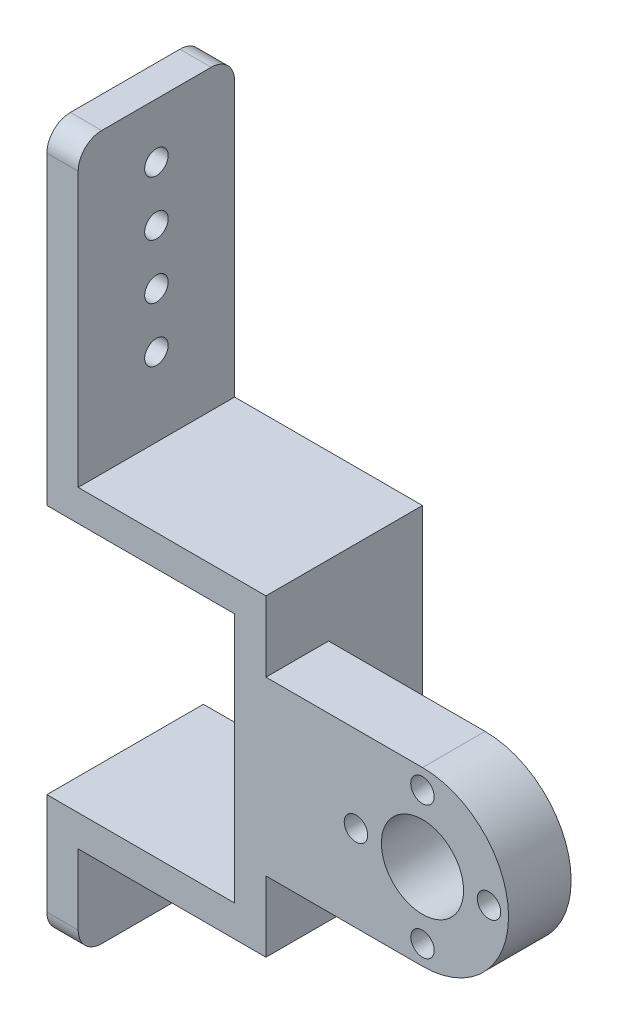
SolidWorks part; units mm, degrees
ref_plane "Front Plane" through (0, 0, 0) normal (0, 0, 1) x (1, 0, 0)
ref_plane "Top Plane" through (0, 0, 0) normal (0, 1, 0) x (1, 0, 0)
ref_plane "Right Plane" through (0, 0, 0) normal (1, 0, 0) x (0, 0, -1)
sketch "Sketch1" plane through (0, 0, 0) normal (0, 0, 1) x (1, 0, 0)
  line L1 (-12, -11) -> (12, -11)
  line L2 (-12, -11) -> (-12, 11)
  line L3 (-12, 11) -> (12, 11)
  line L4 (12, -11) -> (12, 11)
  line L5 (-12, -11) -> (12, 11) construction
  line L6 (-12, 11) -> (12, -11) construction
  circle A0 centre (12, 0) radius 11
  point P0 (0, 0)
  dimension "D1" = 24
  dimension "D2" = 22
extrude "Boss-Extrude2" add sketch "Sketch1" along normal blind 8 contours L4 A0 | L4 A0 | A0 L3 L2 L1
sketch "Sketch3" plane through (0, 0, 8) normal (0, 0, 1) x (1, 0, 0)
  circle A0 centre (12, 0) radius 5.25
  dimension "D1" = 10.5
extrude "Cut-Extrude1" cut sketch "Sketch3" against normal blind 8
sketch "Sketch7" plane through (0, 0, 8) normal (0, 0, 1) x (1, 0, 0)
  line L0 (-12, 11) -> (-12, 20)
  line L1 (-12, 20) -> (-8, 20)
  line L2 (-8, 20) -> (-8, 11)
  line L3 (-12, 11) -> (12, 11) construction
  line L4 (-8, 11) -> (-12, 11)
  line L5 (-12, -11) -> (-12, -20)
  line L6 (-12, -20) -> (-8, -20)
  line L7 (-8, -20) -> (-8, -11)
  line L8 (-12, -11) -> (12, -11) construction
  line L9 (-8, -11) -> (-12, -11)
  dimension "D1" = 9
  dimension "D2" = 4
  dimension "D3" = 9
  dimension "D4" = 4
extrude "Boss-Extrude3" add sketch "Sketch7" against normal blind 8
sketch "Sketch8" plane through (0, 0, 0) normal (0, 0, -1) x (-1, 0, 0)
  line L1 (8, 20) -> (12, 20)
  line L2 (8, 20) -> (8, -20)
  line L3 (8, -20) -> (12, -20)
  line L4 (12, 20) -> (12, -20)
extrude "Boss-Extrude4" add sketch "Sketch8" along normal blind 12
sketch "Sketch9" plane through (-12, 0, 0) normal (-1, 0, 0) x (0, 0, 1)
  line L0 (8, -20) -> (8, 20) construction
  line L1 (-12, 20) -> (8, 20)
  line L2 (-12, 20) -> (-12, 16)
  line L3 (-12, 16) -> (8, 16)
  line L4 (8, 20) -> (8, 16)
  dimension "D1" = 4
extrude "Boss-Extrude5" add sketch "Sketch9" along normal blind 24
sketch "Sketch10" plane through (-12, 0, 0) normal (-1, 0, 0) x (0, 0, 1)
  line L0 (8, -20) -> (8, 16) construction
  line L1 (-12, -20) -> (8, -20)
  line L2 (-12, -20) -> (-12, -16)
  line L3 (-12, -16) -> (8, -16)
  line L4 (8, -20) -> (8, -16)
  dimension "D1" = 4
extrude "Boss-Extrude6" add sketch "Sketch10" along normal blind 24
sketch "Sketch12" plane through (0, 0, -12) normal (0, 0, -1) x (-1, 0, 0)
  line L0 (36, -20) -> (36, 58) construction
  line L2 (36, 20) -> (32, 20)
  line L3 (36, 20) -> (36, 58)
  line L4 (36, 58) -> (32, 58)
  line L5 (32, 20) -> (32, 58)
  dimension "D1" = 78
  dimension "D2" = 4
extrude "Boss-Extrude7" add sketch "Sketch12" against normal blind 20
sketch "Sketch13" plane through (0, -20, 0) normal (0, -1, 0) x (1, 0, 0)
  line L0 (-8, -12) -> (-36, -12) construction
  line L1 (-36, 8) -> (-32, 8)
  line L2 (-36, 8) -> (-36, -12)
  line L3 (-36, -12) -> (-32, -12)
  line L4 (-32, 8) -> (-32, -12)
  dimension "D1" = 4
extrude "Boss-Extrude8" add sketch "Sketch13" along normal blind 12
sketch "Sketch14" plane through (-36, 0, 0) normal (-1, 0, 0) x (0, 0, 1)
  line L0 (8, 58) -> (-12, 58) construction
  circle A0 centre (-2, -27.5) radius 1.5
  dimension "D1" = 3
  dimension "D2" = 85.5
extrude "Cut-Extrude2" cut sketch "Sketch14" against normal blind 12
sketch "Sketch15" plane through (-36, 0, 0) normal (-1, 0, 0) x (0, 0, 1)
  line L0 (8, 58) -> (-12, 58) construction
  circle A0 centre (-2, 51) radius 1.5
  circle A1 centre (-2, 44) radius 1.5
  circle A2 centre (-2, 37) radius 1.5
  circle A3 centre (-2, 30) radius 1.5
  dimension "D1" = 3
  dimension "D2" = 3
  dimension "D3" = 3
  dimension "D4" = 3
  dimension "D5" = 7
  dimension "D6" = 7
  dimension "D7" = 7
  dimension "D8" = 7
extrude "Cut-Extrude3" cut sketch "Sketch15" against normal blind 12
fillet "Fillet1" radius 3 4 edges at (-34, 58, -12) (-34, 58, 8) (-34, -32, -12) (-34, -32, 8)
sketch "Sketch16" plane through (0, 0, 0) normal (0, 0, -1) x (-1, 0, 0)
  line L0 (-12, 5.25) -> (-12, 8.5) construction
  circle A0 centre (-12, 0) radius 5.25 construction
  circle A1 centre (-12, 8.5) radius 1.5
  circle A2 centre (-20.5, 0) radius 1.5
  circle A3 centre (-12, -8.5) radius 1.5
  circle A4 centre (-3.5, 0) radius 1.5
  dimension "D2" = 3
  dimension "D1" = 8.5
  dimension "D3" = 3
  dimension "D4" = 3
  dimension "D5" = 3
  dimension "D6" = 8.5
  dimension "D7" = 8.5
  dimension "D8" = 8.5
extrude "Cut-Extrude4" cut sketch "Sketch16" against normal blind 12
